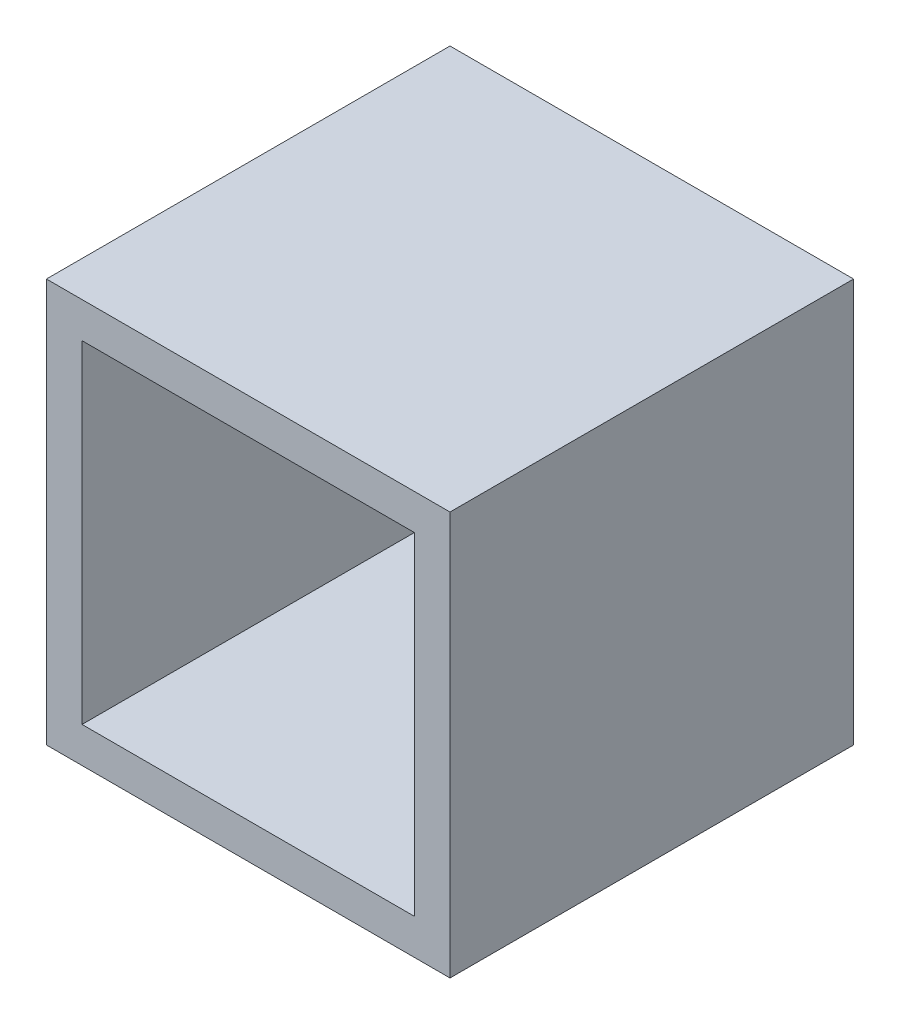
SolidWorks part; units mm, degrees
ref_plane "前视基准面" through (0, 0, 0) normal (0, 0, 1) x (1, 0, 0)
ref_plane "上视基准面" through (0, 0, 0) normal (0, 1, 0) x (1, 0, 0)
ref_plane "右视基准面" through (0, 0, 0) normal (1, 0, 0) x (0, 0, -1)
sketch "草图1" plane through (0, 0, 0) normal (0, 0, 1) x (1, 0, 0)
  line L1 (17, -17) -> (-17, -17)
  line L2 (17, -17) -> (17, 17)
  line L3 (17, 17) -> (-17, 17)
  line L4 (-17, -17) -> (-17, 17)
  line L5 (17, -17) -> (-17, 17) construction
  line L6 (17, 17) -> (-17, -17) construction
  line L7 (14, -14) -> (-14, -14)
  line L8 (14, -14) -> (14, 14)
  line L9 (14, 14) -> (-14, 14)
  line L10 (-14, -14) -> (-14, 14)
  line L11 (14, -14) -> (-14, 14) construction
  line L12 (14, 14) -> (-14, -14) construction
  point P0 (0, 0)
  point P6 (0, 0)
  dimension "D1" = 34
  dimension "D2" = 34
  dimension "D3" = 3
extrude "凸台-拉伸1" add sketch "草图1" along normal blind 34
sketch "草图2" plane through (-14, 0, 0) normal (1, 0, 0) x (0, 0, -1)
  line L0 (-34, -14) -> (0, -14) construction
  line L1 (0, 14) -> (-3, 14)
  line L2 (0, 14) -> (0, -14)
  line L3 (0, -14) -> (-3, -14)
  line L4 (-3, 14) -> (-3, -14)
  dimension "D1" = 3
extrude "凸台-拉伸2" add sketch "草图2" along normal up to next
